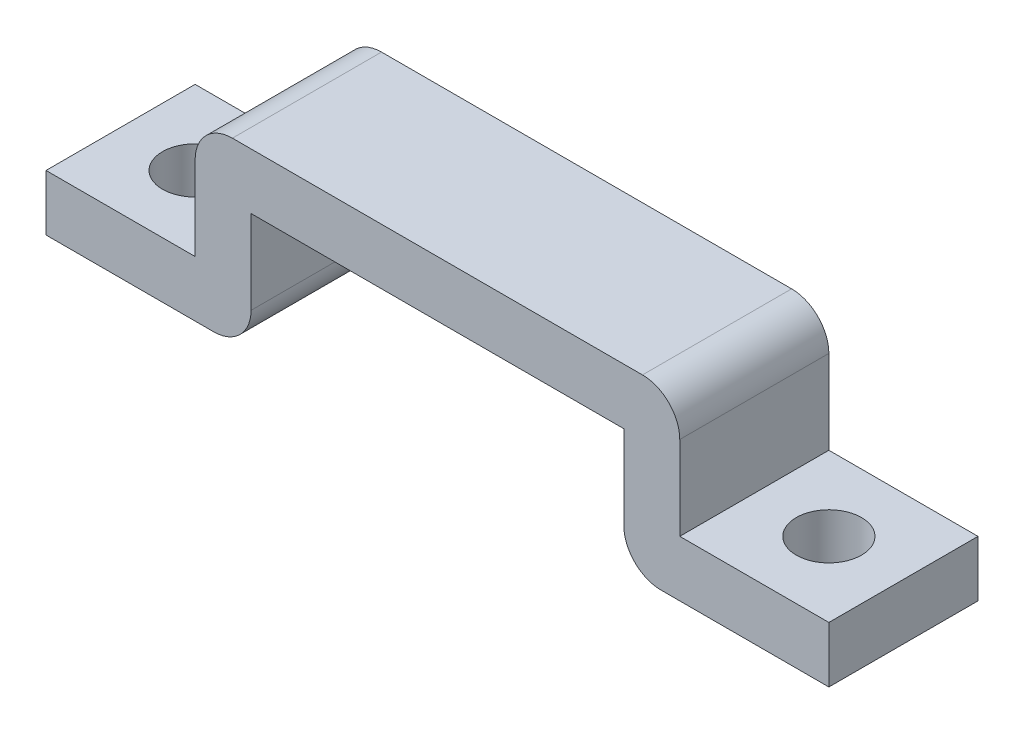
SolidWorks part; units mm, degrees
ref_plane "Front Plane" through (0, 0, 0) normal (0, 0, 1) x (1, 0, 0)
ref_plane "Top Plane" through (0, 0, 0) normal (0, 1, 0) x (1, 0, 0)
ref_plane "Right Plane" through (0, 0, 0) normal (1, 0, 0) x (0, 0, -1)
sketch "Sketch1" plane through (0, 0, 0) normal (0, 0, 1) x (1, 0, 0)
  line L0 (0, 15.8824) -> (0, -15.7941) construction
  line L1 (-21, 0) -> (-12, 0)
  line L2 (-10, 2) -> (-10, 6.5)
  line L3 (-10, 6.5) -> (10, 6.5)
  line L4 (10, 2) -> (10, 6.5)
  line L5 (11, 9.5) -> (-11, 9.5)
  line L6 (-13, 7.5) -> (-13, 3)
  line L7 (-13, 3) -> (-21, 3)
  line L8 (-21, 3) -> (-21, 0)
  line L9 (21, 0) -> (12, 0)
  line L10 (21, 3) -> (21, 0)
  line L11 (13, 3) -> (21, 3)
  line L12 (13, 7.5) -> (13, 3)
  arc A0 (10, 2) -> (12, 0) centre (12, 2) ccw
  arc A1 (-12, 0) -> (-10, 2) centre (-12, 2) ccw
  arc A2 (13, 7.5) -> (11, 9.5) centre (11, 7.5) ccw
  arc A3 (-11, 9.5) -> (-13, 7.5) centre (-11, 7.5) ccw
  point P5 (0, 6.5)
  point P17 (0, 9.5)
  point P19 (10, 0)
  point P22 (-10, 0)
  point P25 (13, 9.5)
  point P28 (-13, 9.5)
  dimension "D7" = 2
  dimension "D1" = 3
  dimension "D2" = 10
  dimension "D3" = 3
  dimension "D4" = 3
  dimension "D5" = 21
  dimension "D6" = 6.5
extrude "Boss-Extrude1" add sketch "Sketch1" along normal blind 8
sketch "Sketch2" plane through (0, 3, 0) normal (0, 1, 0) x (1, 0, 0)
  line L0 (-21, -4) -> (21, -4) construction
  line L1 (-21, -8) -> (-21, 0) construction
  line L2 (21, -8) -> (21, 0) construction
  line L3 (0, 0) -> (0, -8) construction
  line L4 (11, -8) -> (-11, -8) construction
  circle A0 centre (-17, -4) radius 1.75
  circle A1 centre (17, -4) radius 1.75
  dimension "D1" = 3.5
  dimension "D2" = 17
extrude "Cut-Extrude1" cut sketch "Sketch2" against normal through all
